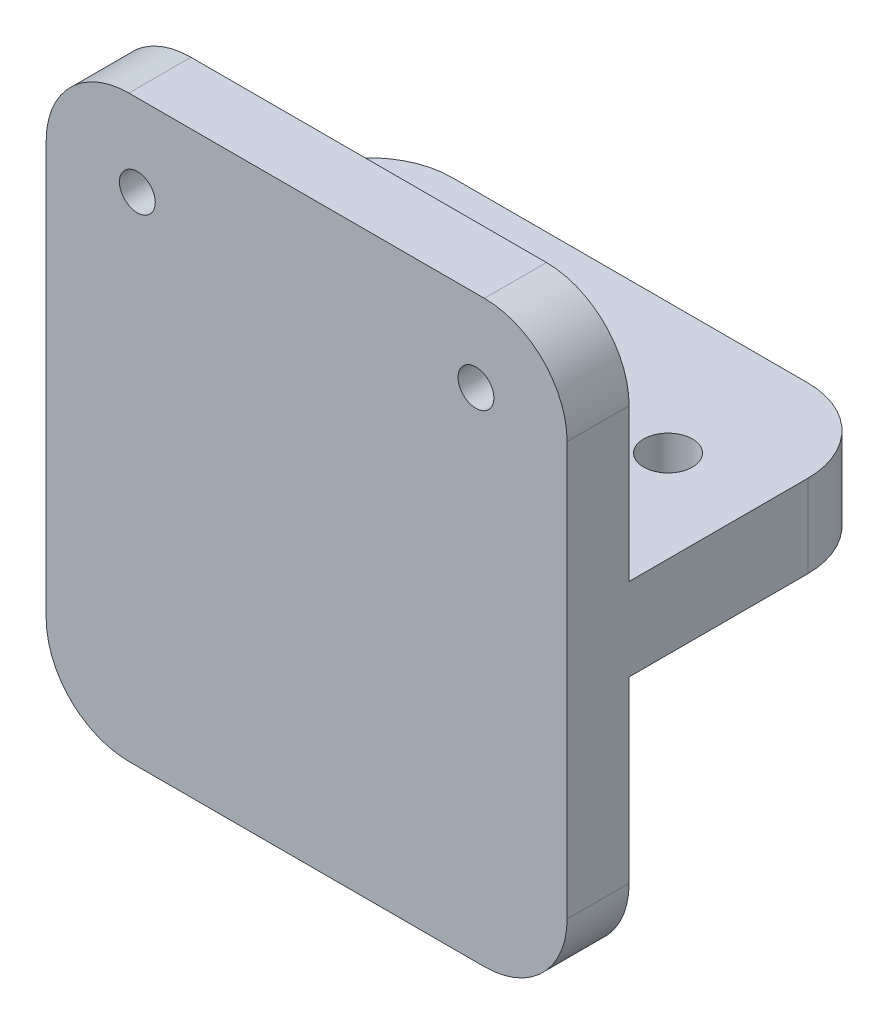
SolidWorks part; units mm, degrees
ref_plane "Front Plane" through (0, 0, 0) normal (0, 0, 1) x (1, 0, 0)
ref_plane "Top Plane" through (0, 0, 0) normal (0, 1, 0) x (1, 0, 0)
ref_plane "Right Plane" through (0, 0, 0) normal (1, 0, 0) x (0, 0, -1)
sketch "Sketch1" plane through (0, 0, 0) normal (0, 0, 1) x (1, 0, 0)
  line L0 (0, 0) -> (0, 22.225) construction
  line L1 (-20, -22.225) -> (20, -22.225)
  line L2 (-20, -22.225) -> (-20, 22.225)
  line L3 (-20, 22.225) -> (20, 22.225)
  line L4 (20, -22.225) -> (20, 22.225)
  line L5 (-20, -22.225) -> (20, 22.225) construction
  line L6 (-20, 22.225) -> (20, -22.225) construction
  line L7 (-13, 15.9587) -> (13, 15.9587) construction
  circle A0 centre (-13, 15.9587) radius 1.375
  circle A1 centre (13, 15.9587) radius 1.375
  point P0 (0, 0)
  point P11 (0, 15.9587)
  dimension "D3" = 2.75
  dimension "D1" = 40
  dimension "D2" = 26
  dimension "D4" = 6.2663
  dimension "D5" = 44.45
extrude "Boss-Extrude1" add sketch "Sketch1" along normal blind 4.7625
sketch "Sketch2" plane through (0, 0, 0) normal (0, 0, -1) x (-1, 0, 0)
  line L0 (-20, -22.225) -> (-20, 22.225) construction
  line L1 (-20, 4.191) -> (20, 4.191)
  line L2 (-20, 4.191) -> (-20, -2.159)
  line L3 (-20, -2.159) -> (20, -2.159)
  line L4 (20, 4.191) -> (20, -2.159)
  line L5 (20, 22.225) -> (20, -22.225) construction
  line L6 (20, -22.225) -> (-20, -22.225) construction
  dimension "D1" = 6.35
  dimension "D2" = 20.066
extrude "Boss-Extrude2" add sketch "Sketch2" along normal blind 20.066
sketch "Sketch3" plane through (0, 4.191, 0) normal (0, 1, 0) x (1, 0, 0)
  line L0 (20, 10.033) -> (-20, 10.033) construction
  line L1 (20, 20.066) -> (20, 0) construction
  line L2 (-20, 20.066) -> (-20, 0) construction
  circle A0 centre (12.954, 10.033) radius 1.875
  circle A1 centre (-12.954, 10.033) radius 1.875
  point P10 (0, 10.033)
  dimension "D1" = 3.75
  dimension "D2" = 25.908
  dimension "D3" = 12.954
extrude "Cut-Extrude1" cut sketch "Sketch3" against normal through all
fillet "Fillet1" radius 6.35 6 edges at (20, -22.225, 2.3813) (-20, -22.225, 2.3813) (-20, 1.016, -20.066) (20, 1.016, -20.066) (20, 22.225, 2.3813) (-20, 22.225, 2.3813)
